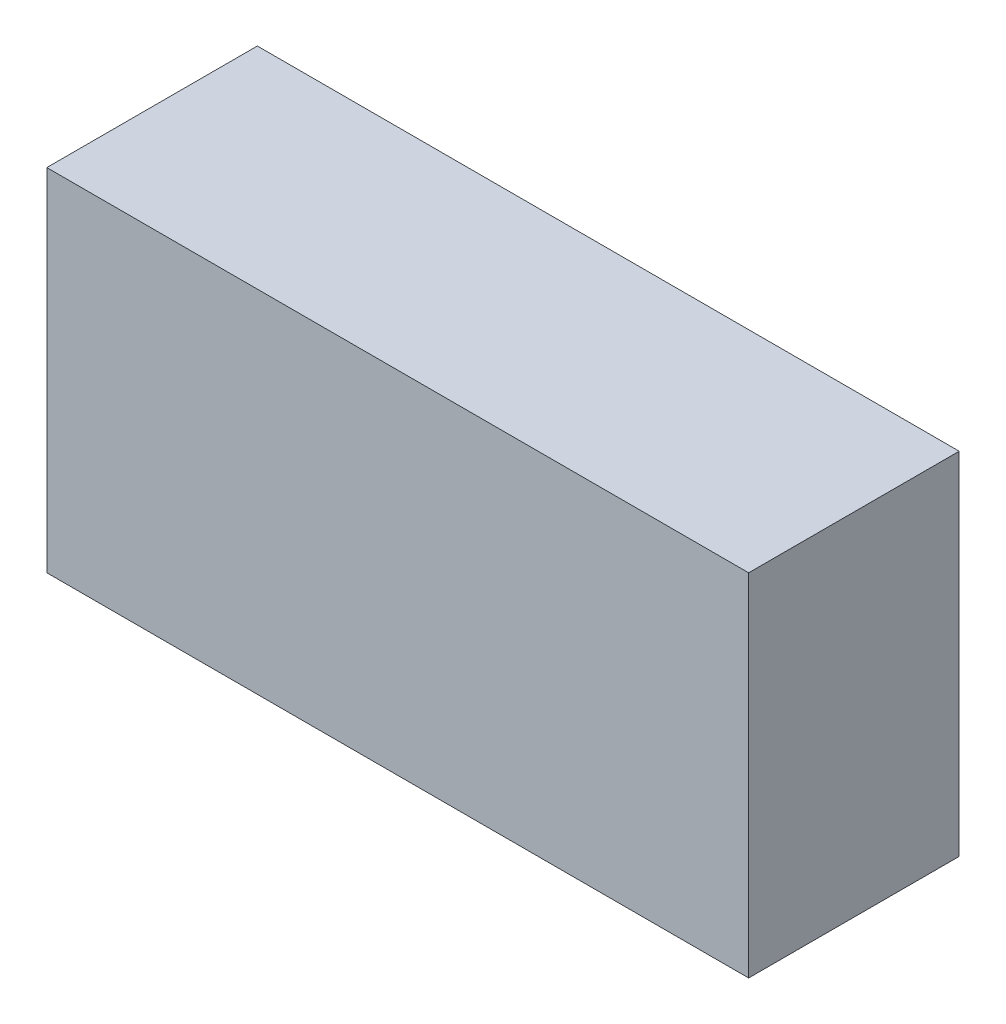
SolidWorks part; units mm, degrees
material "Cedar"
ref_plane "Front Plane" through (0, 0, 0) normal (0, 0, 1) x (1, 0, 0)
ref_plane "Top Plane" through (0, 0, 0) normal (0, 1, 0) x (1, 0, 0)
ref_plane "Right Plane" through (0, 0, 0) normal (1, 0, 0) x (0, 0, -1)
sketch "Sketch1" plane through (0, 0, 0) normal (0, 0, 1) x (1, 0, 0)
  line L1 (-5, -2.5) -> (5, -2.5)
  line L2 (-5, -2.5) -> (-5, 2.5)
  line L3 (-5, 2.5) -> (5, 2.5)
  line L4 (5, -2.5) -> (5, 2.5)
  line L5 (-5, -2.5) -> (5, 2.5) construction
  line L6 (-5, 2.5) -> (5, -2.5) construction
  point P0 (0, 0)
  dimension "D1" = 5
  dimension "D2" = 10
extrude "Boss-Extrude1" add sketch "Sketch1" along normal blind 3
